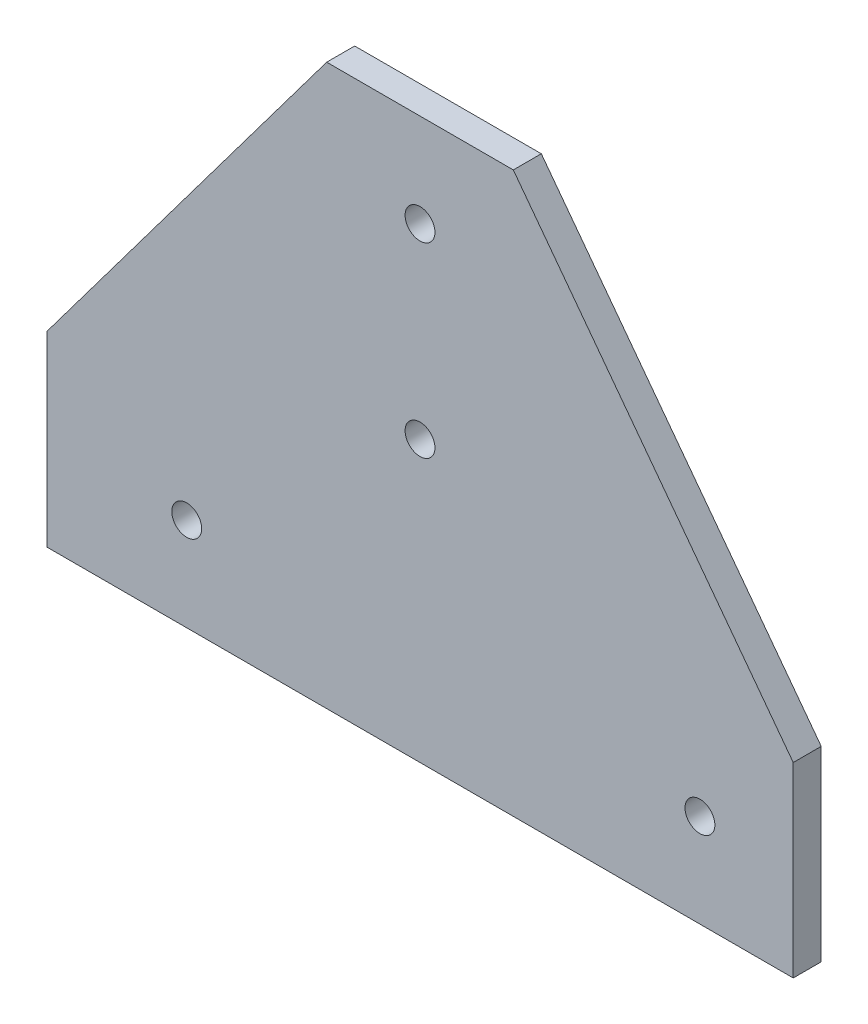
SolidWorks part; units mm, degrees
material "Thornel Mat VMA"
ref_plane "Front Plane" through (0, 0, 0) normal (0, 0, 1) x (1, 0, 0)
ref_plane "Top Plane" through (0, 0, 0) normal (0, 1, 0) x (1, 0, 0)
ref_plane "Right Plane" through (0, 0, 0) normal (1, 0, 0) x (0, 0, -1)
sketch "Sketch1" plane through (0, 0, 0) normal (0, 0, 1) x (1, 0, 0)
  line L0 (453.4899, 0) -> (453.4899, 20)
  line L1 (453.4899, 20) -> (423.4899, 60)
  line L2 (423.4899, 20) -> (423.4899, 260) construction
  line L3 (423.4899, 60) -> (403.4899, 60)
  line L4 (403.4899, 20) -> (403.4899, 260) construction
  line L5 (403.4899, 60) -> (373.4899, 20)
  line L6 (-171.5101, 20) -> (403.4899, 20) construction
  line L7 (373.4899, 20) -> (373.4899, 0)
  line L8 (-221.5101, 0) -> (453.4899, 0) construction
  line L9 (373.4899, 0) -> (453.4899, 0)
  line L10 (423.4899, 20) -> (453.4899, 20) construction
  line L11 (413.4899, 60) -> (413.4899, 0) construction
  line L12 (453.4899, 10) -> (373.4899, 10) construction
  circle A0 centre (413.4899, 50) radius 1.6
  circle A1 centre (413.4899, 30) radius 1.6
  circle A2 centre (443.4899, 10) radius 1.6
  circle A3 centre (388.4899, 10) radius 1.6
  dimension "D3" = 3.2
  dimension "D4" = 10
  dimension "D5" = 20
  dimension "D6" = 15
  dimension "D7" = 10
  dimension "D1" = 40
  dimension "D2" = 40
extrude "Extrude1" add sketch "Sketch1" along normal blind 3
